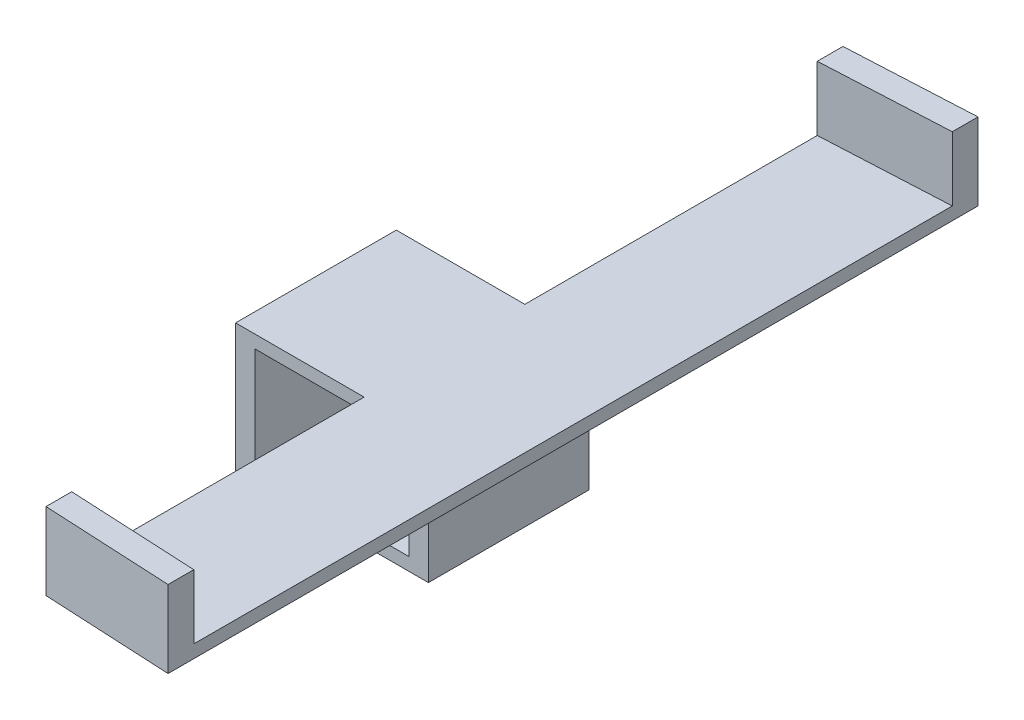
SolidWorks part; units mm, degrees
ref_plane "Front Plane" through (0, 0, 0) normal (0, 0, 1) x (1, 0, 0)
ref_plane "Top Plane" through (0, 0, 0) normal (0, 1, 0) x (1, 0, 0)
ref_plane "Right Plane" through (0, 0, 0) normal (1, 0, 0) x (0, 0, -1)
sketch "Sketch1" plane through (0, 0, 0) normal (0, 1, 0) x (1, 0, 0)
  line L0 (4.6789, 11.5596) -> (4.6789, -13.4404)
  line L1 (-10.3211, 11.5596) -> (19.6789, 11.5596)
  line L2 (-10.3211, 11.5596) -> (-10.3211, -13.4404)
  line L3 (-10.3211, -13.4404) -> (19.6789, -13.4404)
  line L4 (19.6789, 11.5596) -> (19.6789, -13.4404)
  line L5 (-10.3211, -0.9404) -> (19.6789, -0.9404)
  line L6 (-3.0711, 7.5596) -> (12.4289, 7.5596)
  circle A0 centre (-3.0711, 7.5596) radius 1.45
  circle A1 centre (12.4289, 7.5596) radius 1.45
  circle A2 centre (12.4289, -9.4404) radius 1.45
  circle A3 centre (-3.0711, -9.4404) radius 1.45
  point P10 (4.6789, 7.5596)
  dimension "D5" = 2.9
  dimension "D6" = 2.9
  dimension "D7" = 2.9
  dimension "D1" = 30
  dimension "D2" = 25
  dimension "D3" = 15.5
  dimension "D4" = 4
extrude "Boss-Extrude1" add sketch "Sketch1" along normal blind 18
sketch "Sketch2" plane through (0, 18, 0) normal (0, 1, 0) x (1, 0, 0)
sketch "Sketch3" plane through (0, 18, 0) normal (0, 1, 0) x (1, 0, 0)
  line L0 (-10.3211, 11.5596) -> (-10.3211, -13.4404)
  line L1 (-10.3211, -13.4404) -> (19.6789, -13.4404)
  line L2 (19.6789, -13.4404) -> (19.6789, 11.5596)
  line L3 (19.6789, 11.5596) -> (-10.3211, 11.5596)
extrude "Boss-Extrude2" add sketch "Sketch3" along normal blind 2 contours L3 L0 L1 L2
sketch "Sketch4" plane through (0, 0, 13.4404) normal (0, 0, 1) x (1, 0, 0)
  line L2 (16.6789, 2) -> (16.6789, 18)
  line L3 (16.6789, 18) -> (-7.3211, 18)
  line L4 (-7.3211, 2) -> (-7.3211, 18)
  line L5 (-10.3211, 20) -> (19.6789, 20) construction
  line L6 (19.6789, 20) -> (19.6789, 0) construction
  line L7 (-10.3211, 20) -> (-10.3211, 0) construction
  line L8 (-7.3211, 2) -> (16.6789, 2)
  dimension "D1" = 2
  dimension "D2" = 3
  dimension "D3" = 3
extrude "Cut-Extrude2" cut sketch "Sketch4" against normal through all contours L4 L3 L2 L8
sketch "Sketch5" plane through (19.6789, 0, 0) normal (1, 0, 0) x (0, 0, -1)
  line L0 (-13.4404, 18) -> (11.5596, 18)
  line L1 (-13.4404, 20) -> (-13.4404, 0) construction
  line L2 (11.5596, 20) -> (11.5596, 0) construction
  line L3 (-13.4404, 20) -> (11.5596, 20) construction
  line L4 (-13.4404, 18) -> (-13.4404, 20)
  line L5 (-13.4404, 20) -> (11.5596, 20)
  line L6 (11.5596, 20) -> (11.5596, 18)
  dimension "D1" = 2
extrude "Boss-Extrude3" add sketch "Sketch5" along normal blind 10
sketch "Sketch6" plane through (0, 20, 0) normal (0, 1, 0) x (1, 0, 0)
  line L0 (19.6789, 61.5596) -> (19.6789, -63.4404)
  line L1 (29.6789, 11.5596) -> (29.6789, -13.4404) construction
  line L2 (19.6789, 61.5596) -> (29.6789, 62.0645)
  line L3 (29.6789, 62.0645) -> (29.6789, -63.9452)
  line L4 (29.6789, -63.9452) -> (19.6789, -63.4404)
  line L5 (19.6789, -63.4404) -> (9.6789, -62.9355)
  line L6 (19.6789, 61.5596) -> (9.6789, 61.0548)
  line L7 (9.6789, 61.0548) -> (9.6789, -62.9355)
  point P2 (29.6789, -0.9404)
  point P5 (19.6789, -0.9404)
  line M2 (-10.3211, -13.4404) -> (29.6789, -13.4404)
  line M4 (29.6789, 11.5596) -> (-10.3211, 11.5596)
  dimension "D1" = 125
  dimension "D2" = 10
  dimension "D3" = 10
  dimension "D4" = 10
  dimension "D5" = 87.11
  dimension "D6" = 92.89
  dimension "D7" = 87.11
  dimension "D8" = 62.5
extrude "Boss-Extrude4" add sketch "Sketch6" against normal blind 2 contours L6 L7 L0 M4 | L3 L2 L0 M4 | L4 L3 L0 M2 | L7 L5 L0 M2
sketch "Sketch7" plane through (0, 20, 0) normal (0, 1, 0) x (1, 0, 0)
  line L0 (9.6789, 61.0548) -> (29.6789, 62.0645)
  line L1 (29.6789, 62.0645) -> (29.6789, 58.0645)
  line L2 (29.6789, 62.0645) -> (29.6789, -63.9452) construction
  line L3 (29.6789, 58.0645) -> (9.6789, 57.0548)
  line L4 (9.6789, 61.0548) -> (9.6789, 11.5596) construction
  line L5 (9.6789, 57.0548) -> (9.6789, 61.0548)
  line L6 (9.6789, -58.9355) -> (29.6789, -59.9452)
  line L7 (9.6789, -13.4404) -> (9.6789, -62.9355) construction
  line L8 (29.6789, -63.9452) -> (9.6789, -62.9355) construction
  line L9 (9.6789, -58.9355) -> (9.6789, -62.9355)
  line L10 (9.6789, -62.9355) -> (29.6789, -63.9452)
  line L11 (29.6789, -63.9452) -> (29.6789, -59.9452)
  dimension "D1" = 4
  dimension "D2" = 4
  dimension "D3" = 4
extrude "Boss-Extrude5" add sketch "Sketch7" along normal blind 10 contours L5 L0 L1 L3 | L11 L6 L9 L10
